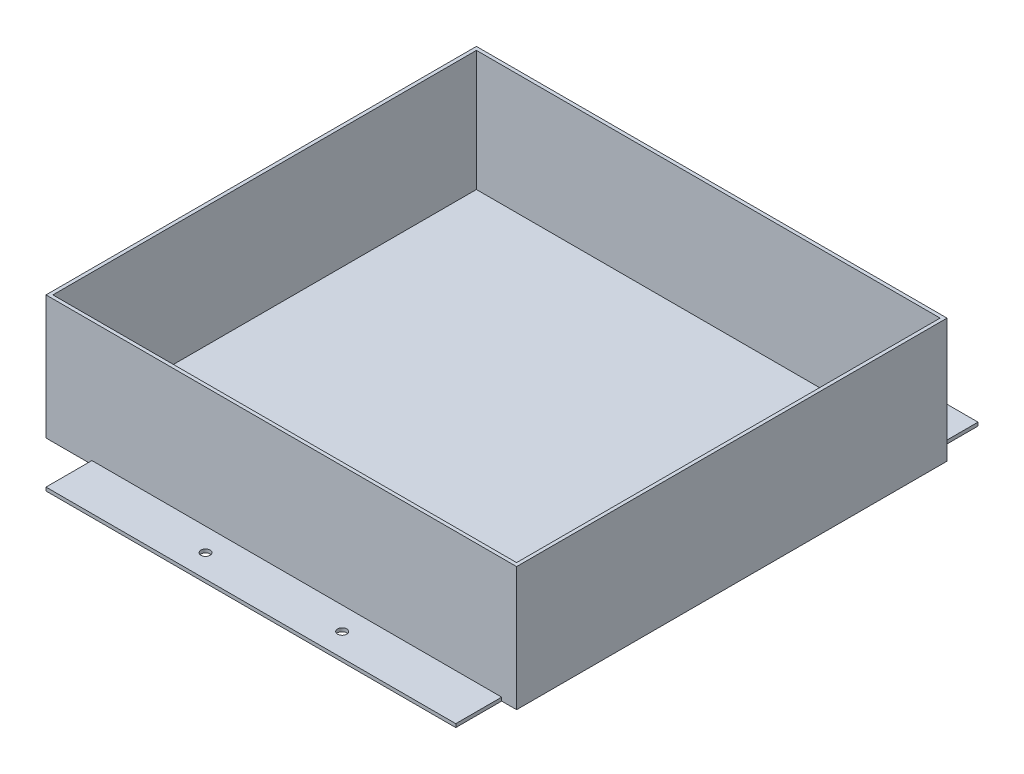
SolidWorks part; units mm, degrees
material "1060 合金"
ref_plane "前基準面" through (0, 0, 0) normal (0, 0, 1) x (1, 0, 0)
ref_plane "上基準面" through (0, 0, 0) normal (0, 1, 0) x (1, 0, 0)
ref_plane "右基準面" through (0, 0, 0) normal (1, 0, 0) x (0, 0, -1)
sketch "草圖1" plane through (0, 0, 0) normal (0, 1, 0) x (1, 0, 0)
  line L0 (0, 0) -> (0, -375)
  line L1 (0, -375) -> (40, -375)
  line L2 (410, -375) -> (410, 0)
  line L3 (410, 0) -> (397, 0)
  line L4 (40, 0) -> (40, 40)
  line L5 (40, 40) -> (397, 40)
  line L6 (397, 40) -> (397, 0)
  line L7 (-160.9734, -187.5) -> (501.8482, -187.5) construction
  line L8 (397, -415) -> (397, -375)
  line L9 (40, -415) -> (397, -415)
  line L10 (40, -375) -> (40, -415)
  line L11 (40, 0) -> (0, 0)
  line L12 (397, -375) -> (410, -375)
  line L13 (-67.6138, 20) -> (443.8517, 20) construction
  circle A0 centre (159, 20) radius 4
  circle A1 centre (278, 20) radius 4
  circle A2 centre (278, -395) radius 4
  circle A3 centre (159, -395) radius 4
  dimension "D7" = 8
  dimension "D8" = 8
  dimension "D1" = 375
  dimension "D2" = 410
  dimension "D3" = 40
  dimension "D4" = 40
  dimension "D5" = 13
  dimension "D6" = 20
  dimension "D9" = 119
  dimension "D10" = 119
extrude "填料-伸長2" add sketch "草圖1" along normal blind 3
sketch "草圖2" plane through (0, 3, 0) normal (0, 1, 0) x (1, 0, 0)
  line L0 (0, 0) -> (0, -375)
  line L1 (0, -375) -> (410, -375)
  line L2 (410, -375) -> (410, 0)
  line L3 (410, 0) -> (0, 0)
  line L4 (407, -3) -> (3, -3)
  line L5 (3, -3) -> (3, -372)
  line L6 (3, -372) -> (407, -372)
  line L7 (407, -372) -> (407, -3)
  dimension "D1" = 3
extrude "填料-伸長3" add sketch "草圖2" along normal blind 105
